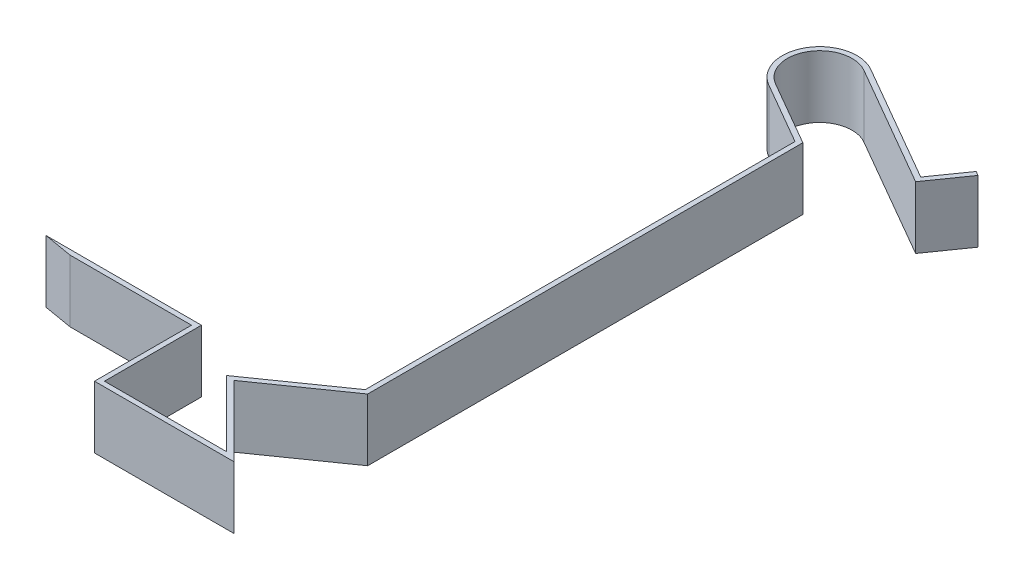
SolidWorks part; units mm, degrees
ref_plane "Front" through (0, 0, 0) normal (0, 0, 1) x (1, 0, 0)
ref_plane "Top" through (0, 0, 0) normal (0, 1, 0) x (1, 0, 0)
ref_plane "Right" through (0, 0, 0) normal (1, 0, 0) x (0, 0, -1)
sketch "草图1" plane through (0, 0, 0) normal (0, 1, 0) x (1, 0, 0)
  line L0 (-57.3117, 0) -> (62.4971, 0) construction
  line L1 (-10.9347, 12.9349) -> (-4.6847, 12.9349)
  line L2 (-4.6847, 12.9349) -> (-4.6847, 9.0349)
  line L3 (-4.6847, 9.0349) -> (0.2324, 9.0349)
  line L4 (0.2324, 9.0349) -> (-2.4231, 11.6904)
  line L8 (-0.1446, 35.3055) -> (4.6185, 32.5555)
  line L9 (4.6185, 32.5555) -> (5.5385, 33.8645)
  line L10 (-10.9347, 12.9349) -> (-9.7677, 12.7349)
  line L11 (-9.7677, 12.7349) -> (-4.8847, 12.7349)
  line L12 (-4.8847, 12.7349) -> (-4.8847, 8.8349)
  line L13 (-4.8847, 8.8349) -> (0.7153, 8.8349)
  line L14 (0.7153, 8.8349) -> (-2.1132, 11.6633)
  line L17 (1.0535, 31.3806) -> (-1.5446, 32.8806)
  line L18 (-0.2446, 35.1323) -> (4.677, 32.2908)
  line L19 (4.677, 32.2908) -> (5.7124, 33.7641)
  line L20 (5.5385, 33.8645) -> (5.7124, 33.7641)
  line L21 (-1.6446, 32.7074) -> (0.8535, 31.2651)
  line L22 (1.0535, 31.3806) -> (1.0535, 13.8806)
  line L23 (1.0535, 13.8806) -> (-2.1132, 11.6633)
  line L24 (-2.4231, 11.6904) -> (0.8535, 13.9847)
  line L25 (0.8535, 13.9847) -> (0.8535, 31.2651)
  arc A0 (-1.6446, 32.7074) -> (-0.1446, 35.3055) centre (-0.8946, 34.0064) cw
  arc A1 (-0.2446, 35.1323) -> (-1.5446, 32.8806) centre (-0.8946, 34.0064) ccw
  point P9 (2.6069, 28.6996)
  point P13 (0.6825, 27.9197)
  point P28 (3.2281, 28.578)
  point P29 (3.0764, 28.578)
  point P30 (0, 0)
  point P31 (0, 0)
  point P32 (1.5053, 28.8057)
  point P33 (1.4777, 28.8787)
  point P34 (0, 0)
  point P35 (0, 0)
  point P36 (9.9219, 32.46)
  point P37 (0, 0)
  dimension "D3" = 0.2
  dimension "D11" = 0.2
  dimension "D12" = 60
  dimension "D21" = 1.5
  dimension "D1" = 0.2
  dimension "D2" = 0.2
  dimension "D4" = 0.2
  dimension "D5" = 4
  dimension "D6" = 0.2
  dimension "D7" = 0.2
  dimension "D8" = 0.2
  dimension "D9" = 0.2
  dimension "D10" = 45
  dimension "D13" = 6.25
  dimension "D14" = 5.4
  dimension "D15" = 4
  dimension "D16" = 17.5
  dimension "D17" = 5.5
  dimension "D18" = 1.6
  dimension "D19" = 3.9
  dimension "D20" = 80
  dimension "D22" = 3
extrude "凸台-拉伸1" add sketch "草图1" along normal blind 2.5
